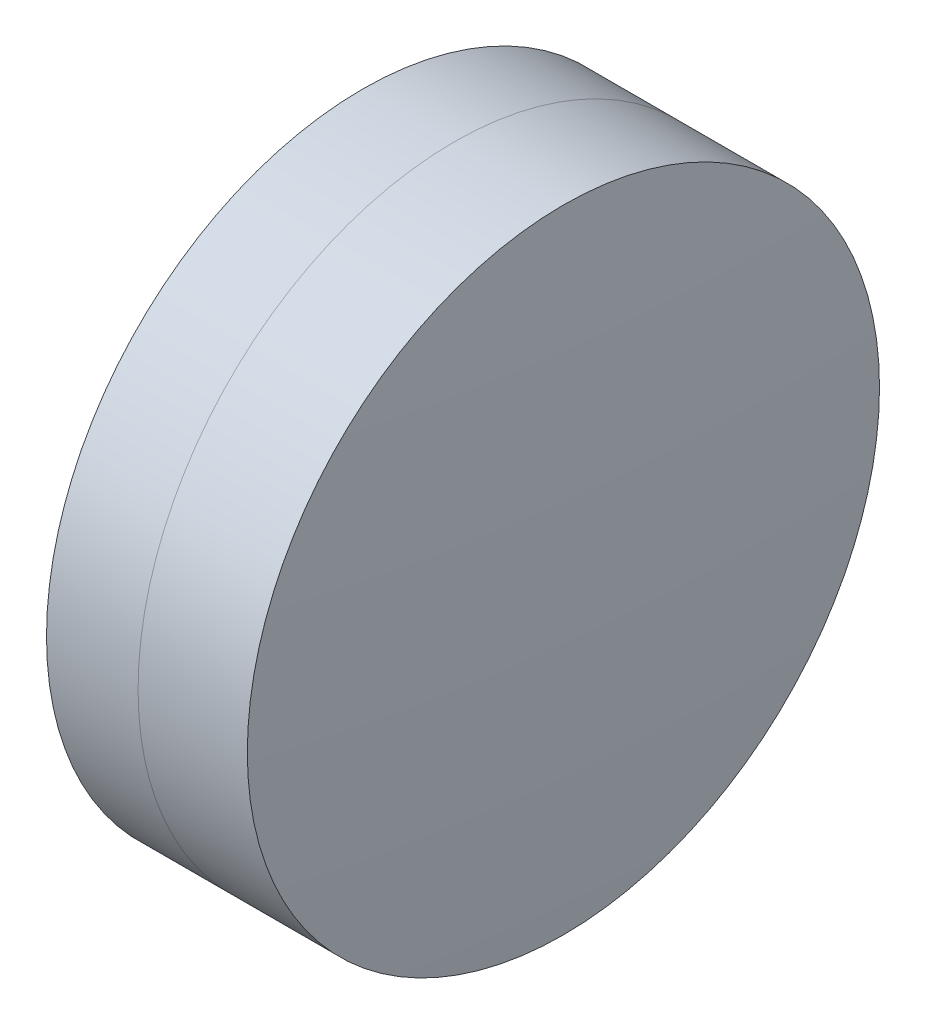
SolidWorks part; units mm, degrees
ref_plane "前视基准面" through (0, 0, 0) normal (0, 0, 1) x (1, 0, 0)
ref_plane "上视基准面" through (0, 0, 0) normal (0, 1, 0) x (1, 0, 0)
ref_plane "右视基准面" through (0, 0, 0) normal (1, 0, 0) x (0, 0, -1)
sketch "草图1" plane through (0, 0, 0) normal (0, 1, 0) x (1, 0, 0)
  line L0 (-9.7026, 0) -> (11.7646, 0) construction
  line L1 (4.1758, -6.35) -> (6.0152, -6.35)
  line L2 (4.1758, 6.35) -> (6.0152, 6.35)
  arc A0 (6.0152, -6.35) -> (6.0152, 6.35) centre (-15.5702, 0) ccw
  arc A1 (4.1758, 6.35) -> (4.1758, -6.35) centre (30.8298, 0) ccw
  point P10 (3.4298, 0)
  point P11 (6.9298, 0)
  dimension "D3" = 27.4
  dimension "D4" = 22.5
  dimension "D1" = 6.35
  dimension "D2" = 6.35
  dimension "D5" = 3.5
revolve "旋转1" add sketch "草图1" angle 360 about L0
sketch "草图2" plane through (0, 0, 0) normal (0, 1, 0) x (1, 0, 0)
  line L0 (-0.5519, 0) -> (13.3053, 0) construction
  line L2 (6.0152, 6.35) -> (8.2099, 6.35)
  line L3 (6.0152, -6.35) -> (8.2099, -6.35)
  arc A0 (8.2099, -6.35) -> (8.2099, 6.35) centre (-83.3702, 0) ccw
  arc A1 (6.0152, -6.35) -> (6.0152, 6.35) centre (-15.5702, 0) ccw construction
  arc A2 (6.0152, -6.35) -> (6.0152, 6.35) centre (-15.5702, 0) ccw
  point P4 (6.9298, 0)
  point P8 (8.4298, 0)
  dimension "D1" = 91.8
  dimension "D2" = 1.5
revolve "旋转3" add sketch "草图2" angle 360 about L0
